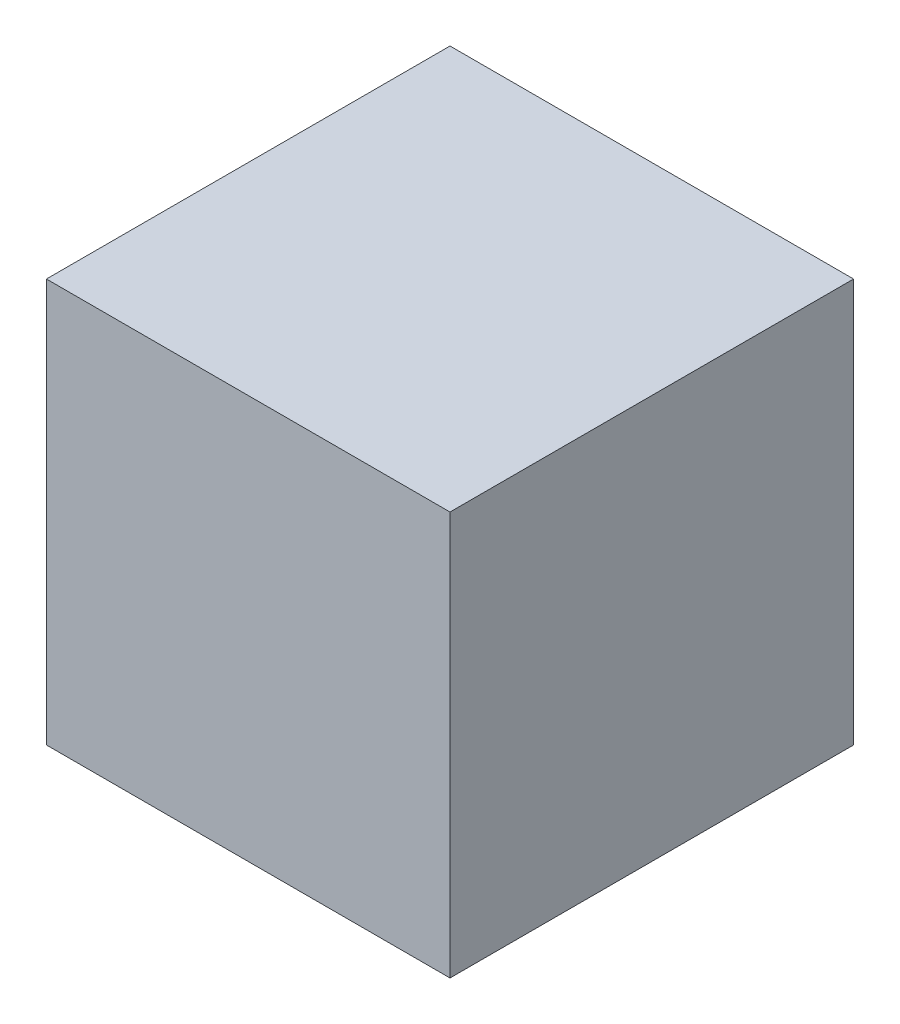
SolidWorks part; units mm, degrees
ref_plane "Ebene vorne" through (0, 0, 0) normal (0, 0, 1) x (1, 0, 0)
ref_plane "Ebene oben" through (0, 0, 0) normal (0, 1, 0) x (1, 0, 0)
ref_plane "Ebene rechts" through (0, 0, 0) normal (1, 0, 0) x (0, 0, -1)
sketch "Skizze1" plane through (0, 0, 0) normal (0, 1, 0) x (1, 0, 0)
  line L0 (0, 29.1723) -> (0, 28.1876) construction
  line L1 (0, 28.1876) -> (0, -23.264) construction
  line L2 (-44.0276, 0) -> (39.4275, 0) construction
  line L4 (-26.5, 26.5) -> (26.5, 26.5)
  line L5 (-26.5, 26.5) -> (-26.5, -26.5)
  line L6 (-26.5, -26.5) -> (26.5, -26.5)
  line L7 (26.5, 26.5) -> (26.5, -26.5)
  line L8 (-26.5, 26.5) -> (26.5, -26.5) construction
  line L9 (-26.5, -26.5) -> (26.5, 26.5) construction
  point P6 (0, 0)
extrude "Aufsatz-Linear austragen3" add sketch "Skizze1" along normal mid plane 53 contours L5 L6 L7 L4
